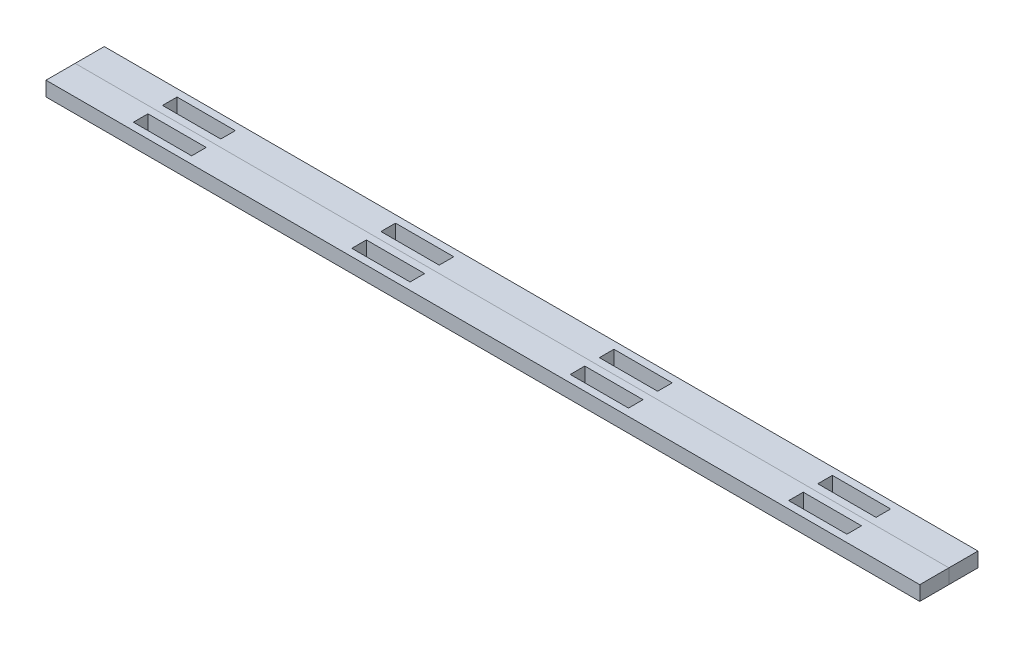
SolidWorks part; units mm, degrees
material "Cedar"
ref_plane "Front Plane" through (0, 0, 0) normal (0, 0, 1) x (1, 0, 0)
ref_plane "Top Plane" through (0, 0, 0) normal (0, 1, 0) x (1, 0, 0)
ref_plane "Right Plane" through (0, 0, 0) normal (1, 0, 0) x (0, 0, -1)
sketch "Sketch1" plane through (0, 0, 0) normal (0, 1, 0) x (1, 0, 0)
  line L1 (-190.5, 6.35) -> (190.5, 6.35)
  line L2 (-190.5, 6.35) -> (-190.5, -6.35)
  line L3 (-190.5, -6.35) -> (190.5, -6.35)
  line L4 (190.5, 6.35) -> (190.5, -6.35)
  line L5 (-190.5, 6.35) -> (190.5, -6.35) construction
  line L6 (-190.5, -6.35) -> (190.5, 6.35) construction
  point P0 (0, 0)
  dimension "D1" = 381
  dimension "D2" = 12.7
extrude "Boss-Extrude1" add sketch "Sketch1" along normal blind 6.35
sketch "Sketch2" plane through (0, 6.35, 0) normal (0, 1, 0) x (1, 0, 0)
  line L0 (-190.5, 0) -> (-155.575, 0) construction
  line L1 (-155.575, 3.175) -> (-130.175, 3.175)
  line L2 (-155.575, 3.175) -> (-155.575, -3.175)
  line L3 (-155.575, -3.175) -> (-130.175, -3.175)
  line L4 (-130.175, 3.175) -> (-130.175, -3.175)
  line L5 (-155.575, 3.175) -> (-130.175, -3.175) construction
  line L6 (-155.575, -3.175) -> (-130.175, 3.175) construction
  line L7 (-190.5, 6.35) -> (-190.5, -6.35) construction
  point P0 (-142.875, 0)
  dimension "D1" = 25.4
  dimension "D2" = 6.35
  dimension "D3" = 34.925
extrude "Cut-Extrude1" cut sketch "Sketch2" against normal through all
pattern_linear "LPattern1" count 4 spacing 95.25 along (1, 0, 0) of "Cut-Extrude1"
pattern_linear "LPattern2" count 2 spacing 12.7 along (0, 0, 1) of bodies 103
